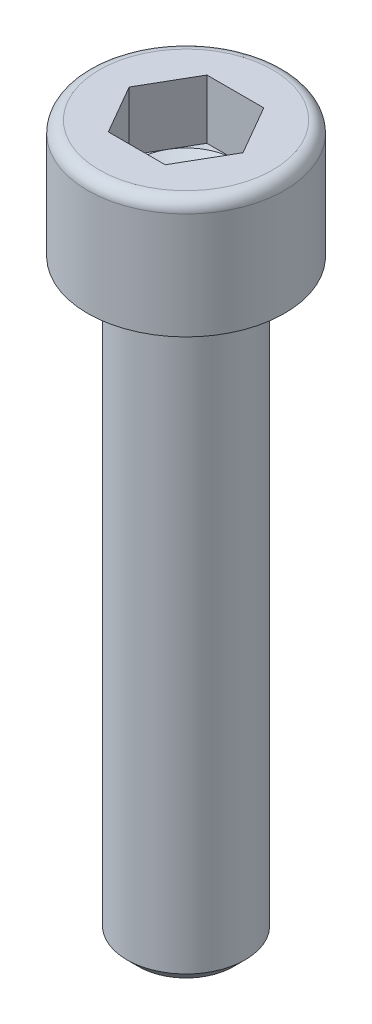
SolidWorks part; units mm, degrees
ref_plane "Plan1" through (0, 0, 0) normal (0, 0, 1) x (1, 0, 0)
ref_plane "Plan2" through (0, 0, 0) normal (0, 1, 0) x (1, 0, 0)
ref_plane "Plan3" through (0, 0, 0) normal (1, 0, 0) x (0, 0, -1)
sketch "Esquisse2" plane through (0, 0, 0) normal (0, 1, 0) x (1, 0, 0)
  circle A0 centre (0, 0) radius 3
  dimension "Diamètre nominal" = 6
extrude "Base-Extrusion" add sketch "Esquisse2" against normal blind 30
chamfer "Chanfrein1" distance 0.6 angle 45
sketch "Esquisse5" plane through (0, 0, 0) normal (0, 0, 1) x (1, 0, 0)
  line L0 (-7.25, 0) -> (2.75, 0) construction
  line L1 (2.5, 6) -> (2.5, 3)
  line L2 (0, 0) -> (5, 0)
  line L3 (0, 0) -> (0, 1.5566)
  line L4 (2.5, 6) -> (4.4, 6)
  line L5 (5, 0) -> (5, 5.4)
  line L6 (2.5, 3) -> (0, 1.5566)
  line L7 (0, 6) -> (0, -30) construction
  line L8 (0, -29.4) -> (0, 0) construction
  line L9 (-2.4, -30) -> (2.4, -30) construction
  line L10 (2.5, 0) -> (-2.5, 0) construction
  arc A0 (5, 5.4) -> (4.4, 6) centre (4.4, 5.4) ccw
  dimension "D2" = 0.6
  dimension "D1" = 5
  dimension "Cote sur plats" = 5
  dimension "D3" = 60
  dimension "D4" = 3
  dimension "Diamètre tête" = 10
  dimension "Diamètre nominal" = 6
  dimension "D5" = 2.5
revolve "Boss.-Révol.1" add sketch "Esquisse5" angle 360 about L7
sketch "Esquisse7" plane through (0, 6, 0) normal (0, 1, 0) x (-1, 0, 0)
  line L0 (0, -2.5) -> (0, 2.5) construction
  line L1 (0, 0) -> (-1.4434, 2.5) construction
  line L2 (0, 0) -> (-2.1651, 1.25) construction
  line L3 (0, 0) -> (-2.8868, 0) construction
  line L4 (1.4434, 2.5) -> (-1.4434, 2.5)
  line L5 (-1.4434, 2.5) -> (-2.8868, 0)
  line L6 (1.4434, -2.5) -> (-1.4434, -2.5)
  line L7 (-1.4434, -2.5) -> (-2.8868, 0)
  line L8 (1.4434, 2.5) -> (2.8868, 0)
  line L9 (1.4434, -2.5) -> (2.8868, 0)
  circle A2 centre (0, 0) radius 2.5 construction
  dimension "D1" = 30
  dimension "D2" = 30
extrude "Enlèv. mat.-Extru.1" cut sketch "Esquisse7" against normal blind 3
equation "\"D1@Chanfrein1\" = \"Diamètre nominal@Esquisse2\"*0.1"
equation "\"D1@Esquisse5\" = \"Diamètre tête@Esquisse5\"/2"
equation "\"D2@Esquisse5\" = \"Diamètre nominal@Esquisse5\"*0.1"
equation "\"D4@Esquisse5\" = \"Diamètre nominal@Esquisse5\"/2"
equation "\"D5@Esquisse5\" = \"Cote sur plats@Esquisse5\"/2"
equation "\"D1@Enlèv. mat.-Extru.1\" = \"Diamètre nominal@Esquisse5\"/2"
